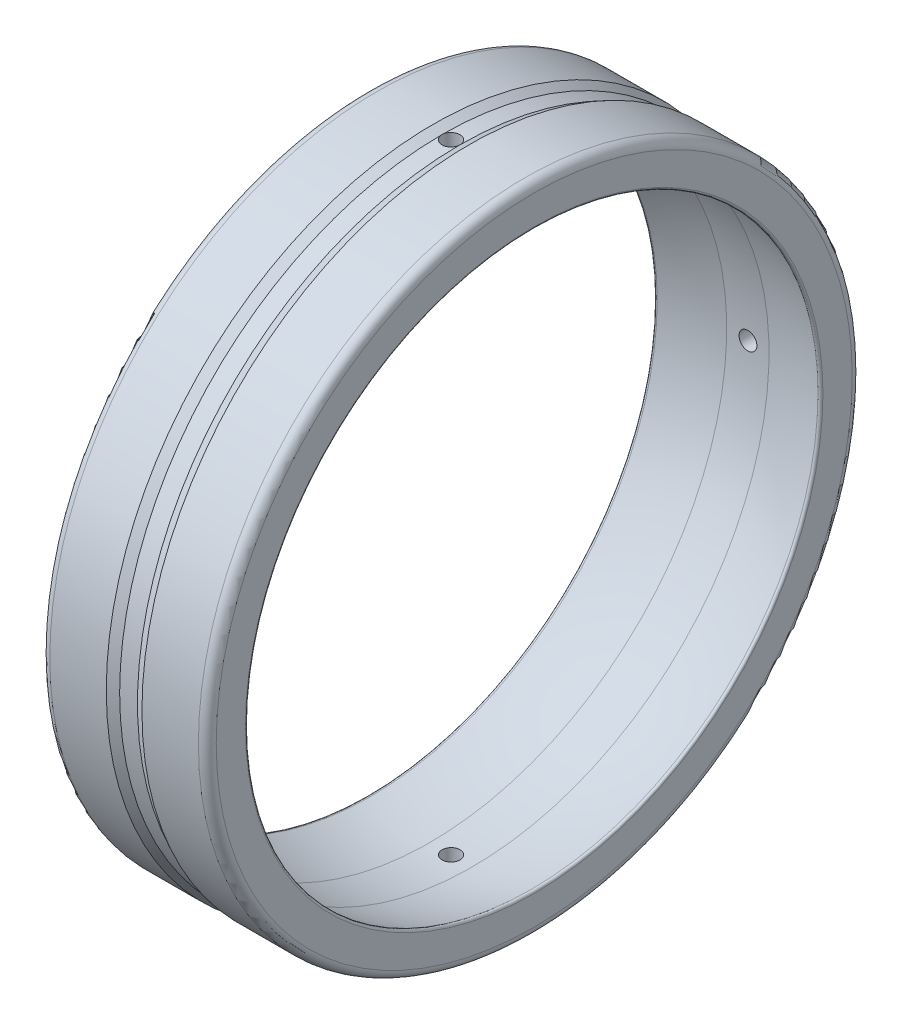
SolidWorks part; units mm, degrees
ref_plane "Front Plane" through (0, 0, 0) normal (0, 0, 1) x (1, 0, 0)
ref_plane "Top Plane" through (0, 0, 0) normal (0, 1, 0) x (1, 0, 0)
ref_plane "Right Plane" through (0, 0, 0) normal (1, 0, 0) x (0, 0, -1)
ref_plane "Plane1" through (0, 0, 0) normal (0, 0, 1) x (1, 0, 0)
sketch "Sketch1" plane through (0, 0, 0) normal (0, 0, 1) x (1, 0, 0)
  line L0 (28, 48.579) -> (28, 53.5)
  line L1 (26.5, 55) -> (17, 55)
  line L2 (17, 55) -> (15.5, 54.25)
  line L3 (15.5, 54.25) -> (12.5, 54.25)
  line L4 (12.5, 54.25) -> (11, 55)
  line L5 (11, 55) -> (1.5, 55)
  line L6 (0, 53.5) -> (0, 48.579)
  line L7 (28, 0) -> (-28, 0) construction
  arc A0 (0, 48.579) -> (0.4765, 48.218) centre (0.375, 48.579) ccw
  arc A1 (0.4765, 48.218) -> (10.4392, 49.9479) centre (13.8846, 0.5519) cw
  arc A2 (10.4392, 49.9479) -> (17.5608, 49.9479) centre (14, -300.034) cw
  arc A3 (17.5608, 49.9479) -> (27.5235, 48.218) centre (14.1154, 0.5519) cw
  arc A4 (27.5235, 48.218) -> (28, 48.579) centre (27.625, 48.579) ccw
  arc A5 (28, 53.5) -> (26.5, 55) centre (26.5, 53.5) ccw
  arc A6 (1.5, 55) -> (0, 53.5) centre (1.5, 53.5) ccw
revolve "Revolve1" add sketch "Sketch1" angle 360 about L7
ref_plane "Plane2" through (0, 0, 0) normal (0, 0, 1) x (1, 0, 0)
sketch "Sketch2" plane through (0, 0, 0) normal (0, 0, 1) x (1, 0, 0)
  line L0 (14, -48.25) -> (15.5, -48.25)
  line L1 (15.5, -48.25) -> (15.5, -55)
  line L2 (15.5, -55) -> (14, -55)
  line L3 (14, -55) -> (14, -48.25)
  line L4 (14, -55) -> (14, -48.25) construction
revolve "Cut-Revolve1" cut sketch "Sketch2" angle 360 about L4
ref_plane "Plane3" through (0, 0, 0) normal (0, 1, 0) x (1, 0, 0)
sketch "Sketch3" plane through (0, 0, 0) normal (0, 1, 0) x (1, 0, 0)
  line L0 (14, 55) -> (15.5, 55)
  line L1 (15.5, 55) -> (15.5, 48.25)
  line L2 (15.5, 48.25) -> (14, 48.25)
  line L3 (14, 48.25) -> (14, 55)
  line L4 (14, 48.25) -> (14, 55) construction
revolve "Cut-Revolve2" cut sketch "Sketch3" angle 360 about L4
ref_plane "Plane4" through (0, 0, 0) normal (0, 0, 1) x (1, 0, 0)
sketch "Sketch4" plane through (0, 0, 0) normal (0, 0, 1) x (1, 0, 0)
  line L0 (14, 55) -> (15.5, 55)
  line L1 (15.5, 55) -> (15.5, 48.25)
  line L2 (15.5, 48.25) -> (14, 48.25)
  line L3 (14, 48.25) -> (14, 55)
  line L4 (14, 48.25) -> (14, 55) construction
revolve "Cut-Revolve3" cut sketch "Sketch4" angle 360 about L4
